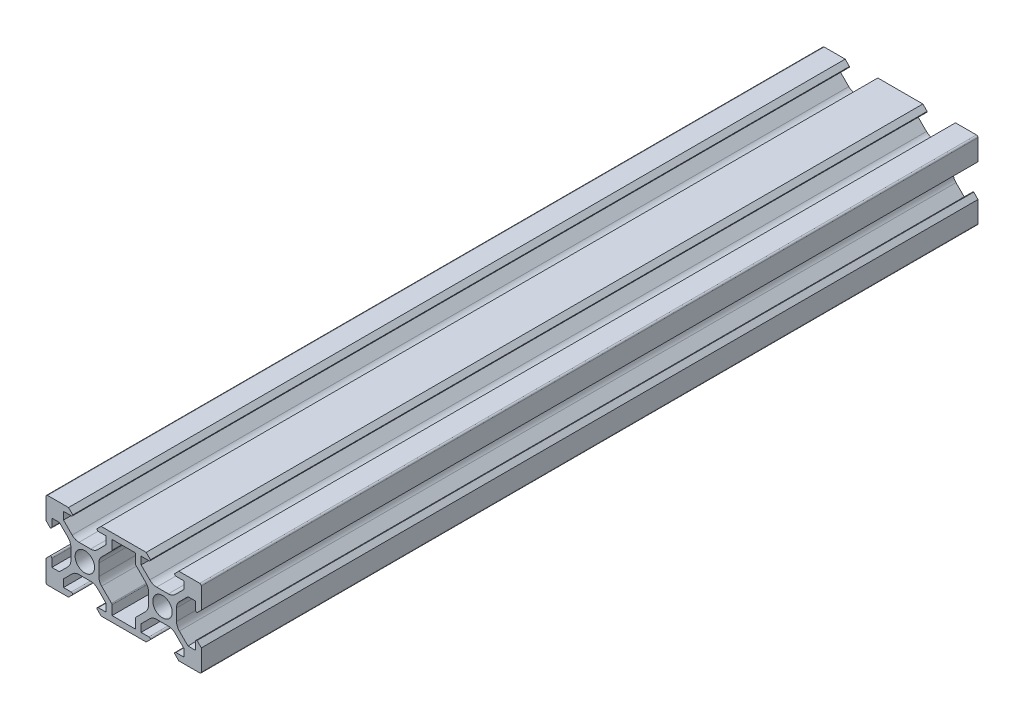
SolidWorks part; units mm, degrees
material "6063-T5"
ref_plane "Plano frontal" through (0, 0, 0) normal (0, 0, 1) x (1, 0, 0)
ref_plane "Plano superior" through (0, 0, 0) normal (0, 1, 0) x (1, 0, 0)
ref_plane "Plano direito" through (0, 0, 0) normal (1, 0, 0) x (0, 0, -1)
sketch "Esboço1" plane through (0, 0, 0) normal (0, 0, 1) x (1, 0, 0)
  line L0 (-13.1, 8.9) -> (-14.2, 10)
  line L1 (-19.6, 10) -> (-14.2, 10)
  line L2 (-13.6, 1.5038) -> (-13.6, 0)
  line L3 (-18.5, 5.5) -> (-18.5, 3.5)
  line L4 (-16.5607, 5.5) -> (-14.3322, 3.2716)
  line L5 (-18.5, 5.5) -> (-16.5607, 5.5)
  line L6 (-20, 9.6) -> (-20, 4.2)
  line L7 (-18.9, 3.1) -> (-20, 4.2)
  line L8 (-3, 8.5) -> (3, 8.5)
  line L9 (-3.1172, 5.8222) -> (-5.6678, 3.2716)
  line L10 (-8.4962, 3.6) -> (-10, 3.6)
  line L11 (-8.2322, 1.7678) -> (-10, 0) construction
  line L12 (-4.5, 6.5607) -> (-6.7284, 4.3322)
  line L13 (-15.5, 8.5) -> (-15.5, 6.5607)
  line L14 (-4.5, 8.5) -> (-4.5, 6.5607)
  line L15 (0, 0) -> (0, 8.5) construction
  line L16 (-6.9, 8.9) -> (-5.8, 10)
  line L17 (-6.4, 0) -> (6.4, 0) construction
  line L18 (-3, -8.5) -> (-3, -6.105)
  line L19 (-18.5, 8.5) -> (-18.5, -8.5) construction
  line L20 (-3.1172, -5.8222) -> (-5.6678, -3.2716)
  line L21 (-6.4, 1.5038) -> (-6.4, 0)
  line L22 (-5.8, -10) -> (5.8, -10)
  line L23 (-19.8828, 9.8828) -> (-10, 0) construction
  line L24 (-6.9, -8.9) -> (-5.8, -10)
  line L25 (-15.5, 6.5607) -> (-13.2716, 4.3322)
  line L26 (-3, -8.5) -> (3, -8.5)
  line L27 (-20, 10) -> (-20, -10) construction
  line L28 (-6.4, -1.5038) -> (-6.4, 0)
  line L29 (19.8828, -9.8828) -> (10, 0) construction
  line L30 (8.2322, -1.7678) -> (10, 0) construction
  line L31 (19.8828, 9.8828) -> (10, 0) construction
  line L32 (8.2322, 1.7678) -> (10, 0) construction
  line L33 (-15.5, 8.5) -> (-13.5, 8.5)
  line L34 (6.5, 8.5) -> (4.5, 8.5)
  line L35 (-4.5, -8.5) -> (-4.5, -6.5607)
  line L36 (-20, 10) -> (0, 10) construction
  line L37 (-4.5, -6.5607) -> (-6.7284, -4.3322)
  line L38 (-4.5, -8.5) -> (-6.5, -8.5)
  line L39 (-18.5, 8.5) -> (-1.5, 8.5) construction
  line L40 (-11.5038, 3.6) -> (-10, 3.6)
  line L41 (-8.4962, -3.6) -> (-10, -3.6)
  line L42 (-8.2322, -1.7678) -> (-10, 0) construction
  line L43 (-18.9, -3.1) -> (-20, -4.2)
  line L44 (-20, -9.6) -> (-20, -4.2)
  line L45 (-11.5038, -3.6) -> (-10, -3.6)
  line L46 (-15.5, -8.5) -> (-13.5, -8.5)
  line L47 (-15.5, -6.5607) -> (-13.2716, -4.3322)
  line L48 (-15.5, -8.5) -> (-15.5, -6.5607)
  line L49 (-19.6, -10) -> (-14.2, -10)
  line L50 (-13.1, -8.9) -> (-14.2, -10)
  line L51 (-18.5, -5.5) -> (-16.5607, -5.5)
  line L52 (-16.5607, -5.5) -> (-14.3322, -3.2716)
  line L53 (-18.5, -5.5) -> (-18.5, -3.5)
  line L54 (0, 10) -> (0, -10) construction
  line L55 (-20, -10) -> (0, -10) construction
  line L56 (-13.6, -1.5038) -> (-13.6, 0)
  line L57 (-18.5, -8.5) -> (-1.5, -8.5) construction
  line L58 (-1.5, 8.5) -> (-1.5, -8.5) construction
  line L59 (-19.8828, -9.8828) -> (-10, 0) construction
  line L60 (3, 8.5) -> (3, 6.105)
  line L61 (-3, 8.5) -> (-3, 6.105)
  line L62 (-6.5, 8.5) -> (-4.5, 8.5)
  line L63 (-5.8, 10) -> (5.8, 10)
  line L64 (13.6, -1.5038) -> (13.6, 0)
  line L65 (18.5, -5.5) -> (18.5, -3.5)
  line L66 (16.5607, -5.5) -> (14.3322, -3.2716)
  line L67 (18.5, -5.5) -> (16.5607, -5.5)
  line L68 (13.1, -8.9) -> (14.2, -10)
  line L69 (19.6, -10) -> (14.2, -10)
  line L70 (15.5, -8.5) -> (15.5, -6.5607)
  line L71 (15.5, -6.5607) -> (13.2716, -4.3322)
  line L72 (15.5, -8.5) -> (13.5, -8.5)
  line L73 (11.5038, -3.6) -> (10, -3.6)
  line L74 (20, -9.6) -> (20, -4.2)
  line L75 (18.9, -3.1) -> (20, -4.2)
  line L76 (8.4962, -3.6) -> (10, -3.6)
  line L77 (11.5038, 3.6) -> (10, 3.6)
  line L78 (4.5, -8.5) -> (6.5, -8.5)
  line L79 (4.5, -6.5607) -> (6.7284, -4.3322)
  line L80 (4.5, -8.5) -> (4.5, -6.5607)
  line L81 (15.5, 8.5) -> (13.5, 8.5)
  line L82 (6.4, -1.5038) -> (6.4, 0)
  line L83 (15.5, 6.5607) -> (13.2716, 4.3322)
  line L84 (6.9, -8.9) -> (5.8, -10)
  line L85 (6.4, 1.5038) -> (6.4, 0)
  line L86 (3.1172, -5.8222) -> (5.6678, -3.2716)
  line L87 (3, -8.5) -> (3, -6.105)
  line L88 (6.9, 8.9) -> (5.8, 10)
  line L89 (4.5, 8.5) -> (4.5, 6.5607)
  line L90 (15.5, 8.5) -> (15.5, 6.5607)
  line L91 (4.5, 6.5607) -> (6.7284, 4.3322)
  line L92 (8.4962, 3.6) -> (10, 3.6)
  line L93 (3.1172, 5.8222) -> (5.6678, 3.2716)
  line L94 (18.9, 3.1) -> (20, 4.2)
  line L95 (20, 9.6) -> (20, 4.2)
  line L96 (18.5, 5.5) -> (16.5607, 5.5)
  line L97 (16.5607, 5.5) -> (14.3322, 3.2716)
  line L98 (18.5, 5.5) -> (18.5, 3.5)
  line L99 (13.6, 1.5038) -> (13.6, 0)
  line L100 (19.6, 10) -> (14.2, 10)
  line L101 (13.1, 8.9) -> (14.2, 10)
  arc A0 (-10, 2.5) -> (-12.5, 0) centre (-10, 0) ccw
  arc A1 (-13.5, 8.5) -> (-13.1, 8.9) centre (-13.5, 8.9) ccw
  arc A2 (-19.6, 10) -> (-20, 9.6) centre (-19.6, 9.6) ccw
  arc A3 (-13.2716, 4.3322) -> (-11.5038, 3.6) centre (-11.5038, 6.1) ccw
  arc A4 (-14.3322, 3.2716) -> (-13.6, 1.5038) centre (-16.1, 1.5038) cw
  arc A5 (-18.5, 3.5) -> (-18.9, 3.1) centre (-18.9, 3.5) cw
  arc A6 (-7.5, 0) -> (-10, 2.5) centre (-10, 0) ccw
  arc A7 (-3, -6.105) -> (-3.1172, -5.8222) centre (-3.4, -6.105) ccw
  arc A8 (-3.1172, 5.8222) -> (-3, 6.105) centre (-3.4, 6.105) ccw
  arc A9 (-5.6678, 3.2716) -> (-6.4, 1.5038) centre (-3.9, 1.5038) ccw
  arc A10 (-6.7284, 4.3322) -> (-8.4962, 3.6) centre (-8.4962, 6.1) cw
  arc A11 (-6.5, 8.5) -> (-6.9, 8.9) centre (-6.5, 8.9) cw
  arc A12 (-10, -2.5) -> (-7.5, 0) centre (-10, 0) ccw
  arc A13 (-6.5, -8.5) -> (-6.9, -8.9) centre (-6.5, -8.9) ccw
  arc A14 (13.5, -8.5) -> (13.1, -8.9) centre (13.5, -8.9) ccw
  arc A15 (-6.7284, -4.3322) -> (-8.4962, -3.6) centre (-8.4962, -6.1) ccw
  arc A16 (-5.6678, -3.2716) -> (-6.4, -1.5038) centre (-3.9, -1.5038) cw
  arc A17 (13.2716, -4.3322) -> (11.5038, -3.6) centre (11.5038, -6.1) ccw
  arc A18 (-12.5, 0) -> (-10, -2.5) centre (-10, 0) ccw
  arc A19 (-18.5, -3.5) -> (-18.9, -3.1) centre (-18.9, -3.5) ccw
  arc A20 (-20, -9.6) -> (-19.6, -10) centre (-19.6, -9.6) ccw
  arc A21 (-14.3322, -3.2716) -> (-13.6, -1.5038) centre (-16.1, -1.5038) ccw
  arc A22 (-13.2716, -4.3322) -> (-11.5038, -3.6) centre (-11.5038, -6.1) cw
  arc A23 (-13.5, -8.5) -> (-13.1, -8.9) centre (-13.5, -8.9) cw
  arc A24 (14.3322, -3.2716) -> (13.6, -1.5038) centre (16.1, -1.5038) cw
  arc A25 (20, -9.6) -> (19.6, -10) centre (19.6, -9.6) cw
  arc A26 (18.5, -3.5) -> (18.9, -3.1) centre (18.9, -3.5) cw
  arc A27 (12.5, 0) -> (10, -2.5) centre (10, 0) cw
  arc A28 (5.6678, -3.2716) -> (6.4, -1.5038) centre (3.9, -1.5038) ccw
  arc A29 (6.7284, -4.3322) -> (8.4962, -3.6) centre (8.4962, -6.1) cw
  arc A30 (6.5, -8.5) -> (6.9, -8.9) centre (6.5, -8.9) cw
  arc A31 (10, -2.5) -> (7.5, 0) centre (10, 0) cw
  arc A32 (6.5, 8.5) -> (6.9, 8.9) centre (6.5, 8.9) ccw
  arc A33 (6.7284, 4.3322) -> (8.4962, 3.6) centre (8.4962, 6.1) ccw
  arc A34 (5.6678, 3.2716) -> (6.4, 1.5038) centre (3.9, 1.5038) cw
  arc A35 (3.1172, 5.8222) -> (3, 6.105) centre (3.4, 6.105) cw
  arc A36 (3, -6.105) -> (3.1172, -5.8222) centre (3.4, -6.105) cw
  arc A37 (7.5, 0) -> (10, 2.5) centre (10, 0) cw
  arc A38 (18.5, 3.5) -> (18.9, 3.1) centre (18.9, 3.5) ccw
  arc A39 (14.3322, 3.2716) -> (13.6, 1.5038) centre (16.1, 1.5038) ccw
  arc A40 (13.2716, 4.3322) -> (11.5038, 3.6) centre (11.5038, 6.1) cw
  arc A41 (19.6, 10) -> (20, 9.6) centre (19.6, 9.6) cw
  arc A42 (13.5, 8.5) -> (13.1, 8.9) centre (13.5, 8.9) cw
  arc A43 (10, 2.5) -> (12.5, 0) centre (10, 0) cw
  point P116 (-10, 0)
  point P168 (0, 10)
  point P183 (0, -8.5)
  point P185 (0, -10)
  dimension "D4" = 2.5
  dimension "D1" = 0.4
  dimension "D3" = 0.4
  dimension "D5" = 0.4
  dimension "D2" = 45
extrude "Ressalto-extrusão1" add sketch "Esboço1" along normal mid plane 200
